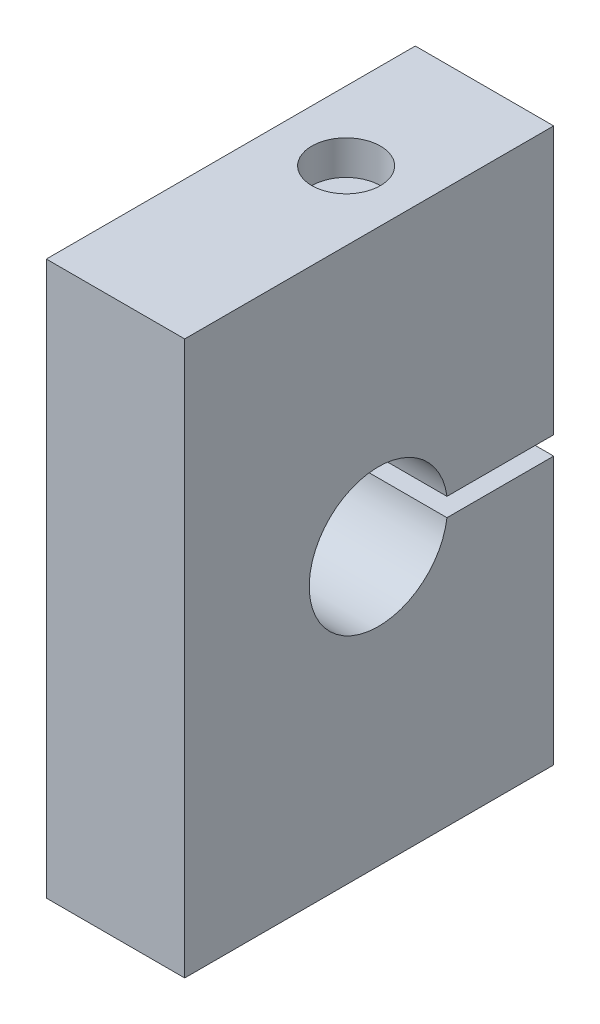
SolidWorks part; units mm, degrees
material "6061 Alloy"
ref_plane "Front Plane" through (0, 0, 0) normal (0, 0, 1) x (1, 0, 0)
ref_plane "Top Plane" through (0, 0, 0) normal (0, 1, 0) x (1, 0, 0)
ref_plane "Right Plane" through (0, 0, 0) normal (1, 0, 0) x (0, 0, -1)
sketch "Sketch2" plane through (0, 0, 0) normal (1, 0, 0) x (0, 0, -1)
  line L0 (0, 38.1) -> (26.67, 38.1) construction
  line L1 (0, 0) -> (50.8, 0)
  line L2 (0, 0) -> (0, 76.2)
  line L3 (0, 76.2) -> (50.8, 76.2)
  line L4 (50.8, 0) -> (50.8, 36.83)
  line L5 (26.67, 38.1) -> (50.8, 38.1) construction
  line L6 (36.11, 36.83) -> (50.8, 36.83)
  line L7 (36.11, 39.37) -> (50.8, 39.37)
  line L8 (50.8, 39.37) -> (50.8, 76.2)
  line L9 (26.67, 39.37) -> (50.8, 39.37) construction
  line L10 (26.67, 36.83) -> (50.8, 36.83) construction
  arc A0 (36.11, 39.37) -> (36.11, 36.83) centre (26.67, 38.1) ccw
  dimension "D4" = 19.05
  dimension "D1" = 76.2
  dimension "D2" = 50.8
  dimension "D3" = 26.67
  dimension "D5" = 1.27
  dimension "D6" = 1.27
extrude "Boss-Extrude1" add sketch "Sketch2" along normal blind 19.05
sketch "Sketch3" plane through (0, 76.2, 0) normal (0, 1, 0) x (1, 0, 0)
  line L0 (9.525, 0) -> (9.525, 31.75) construction
  line L1 (19.05, 0) -> (0, 0) construction
  line L2 (9.525, 31.75) -> (9.525, 50.8) construction
  line L3 (19.05, 50.8) -> (0, 50.8) construction
  line L4 (9.525, 27.0256) -> (9.525, 36.4744)
  arc A0 (9.525, 27.0256) -> (9.525, 36.4744) centre (9.525, 31.75) cw
  circle A1 centre (9.525, 31.75) radius 4.7244
  dimension "D2" = 4.7244
  dimension "D1" = 31.75
sketch "Sketch4" plane through (0, 0, 0) normal (0, -1, 0) x (1, 0, 0)
  line L0 (9.525, 0) -> (9.525, -12.7) construction
  line L1 (19.05, 0) -> (0, 0) construction
  line L2 (9.525, -12.7) -> (9.525, -38.1) construction
  line L3 (9.525, -38.1) -> (9.525, -50.8) construction
  line L4 (19.05, -50.8) -> (0, -50.8) construction
  dimension "D1" = 25.4
hole_wizard "1/4-20 Tapped Hole1" positions "Sketch5" profile "Sketch6" tap size "1/4-20" standard "ANSI Inch"
sketch "Sketch5" plane through (0, 0, 0) normal (0, -1, 0) x (-1, 0, 0)
  point P0 (-9.525, 12.7)
  point P3 (-9.525, 38.1)
sketch "Sketch6" plane through (9.525, 0, -12.7) normal (1, 0, 0) x (0, 0, -1)
  line L0 (0, 0) -> (0, 18.0438)
  line L1 (0, 18.0438) -> (2.5527, 16.51)
  line L2 (2.5527, 16.51) -> (2.5527, 0.635)
  line L3 (2.5527, 0.635) -> (3.1877, 0)
  line L5 (3.1877, 0) -> (0, 0)
  line L6 (-2.5527, 0.635) -> (-3.1877, 0) construction
  line L10 (0, 18.0438) -> (-2.5527, 16.51) construction
  line L11 (0, -6.35) -> (0, 107.95) construction
  dimension "Tap Drill Dia." = 5.1054
  dimension "Tap Drill Depth" = 16.51
  dimension "Near C'Sink Dia." = 6.3754
  dimension "Near C'Sink Angle" = 90
  dimension "Drill Angle" = 118
cosmetic thread "Hole Thread1" parameters "D1"=12.7, "D2"=6.35
cosmetic thread "Hole Thread2" parameters "D1"=12.7, "D2"=6.35
extrude "Cut-Extrude1" cut sketch "Sketch3" against normal blind 4.7244 contours A1
